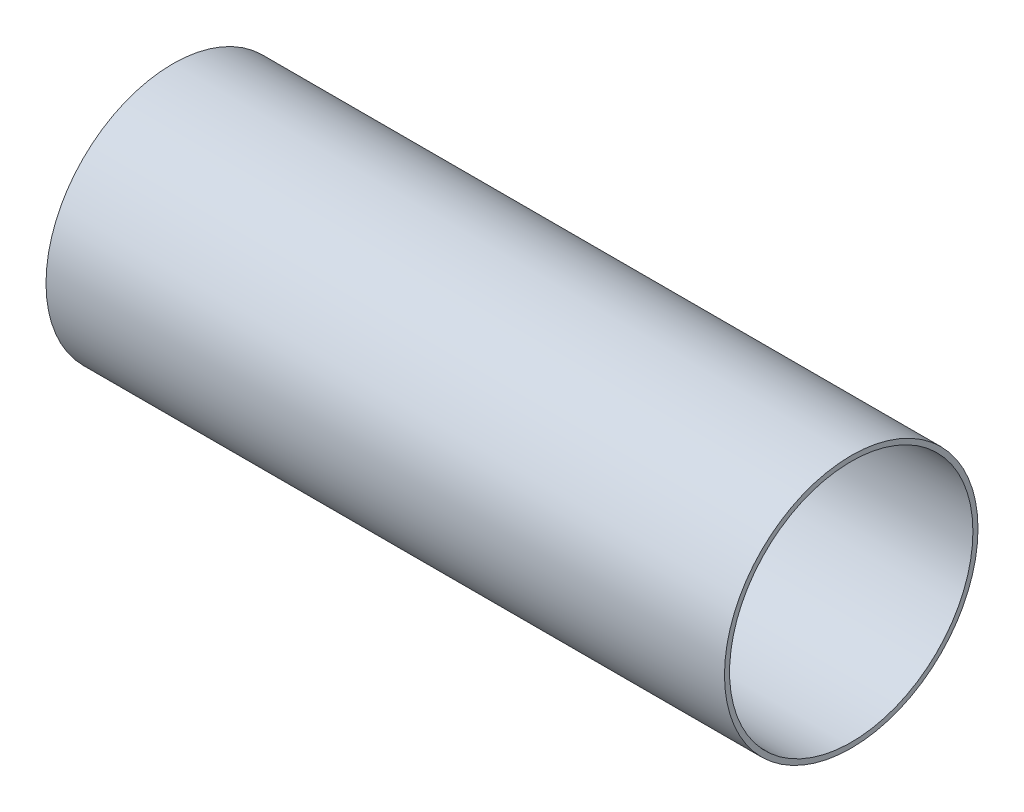
SolidWorks part; units mm, degrees
material "Wildman Fiberglass"
ref_plane "Front Plane" through (0, 0, 0) normal (0, 0, 1) x (1, 0, 0)
ref_plane "Top Plane" through (0, 0, 0) normal (0, 1, 0) x (1, 0, 0)
ref_plane "Right Plane" through (0, 0, 0) normal (1, 0, 0) x (0, 0, -1)
sketch "Sketch1" plane through (0, 0, 0) normal (1, 0, 0) x (0, 0, -1)
  circle A0 centre (0, 0) radius 28.4734
  circle A1 centre (0, 0) radius 27.3304
  dimension "D1" = 56.9468
  dimension "D2" = 54.6608
extrude "Boss-Extrude1" add sketch "Sketch1" along normal blind 152.4
